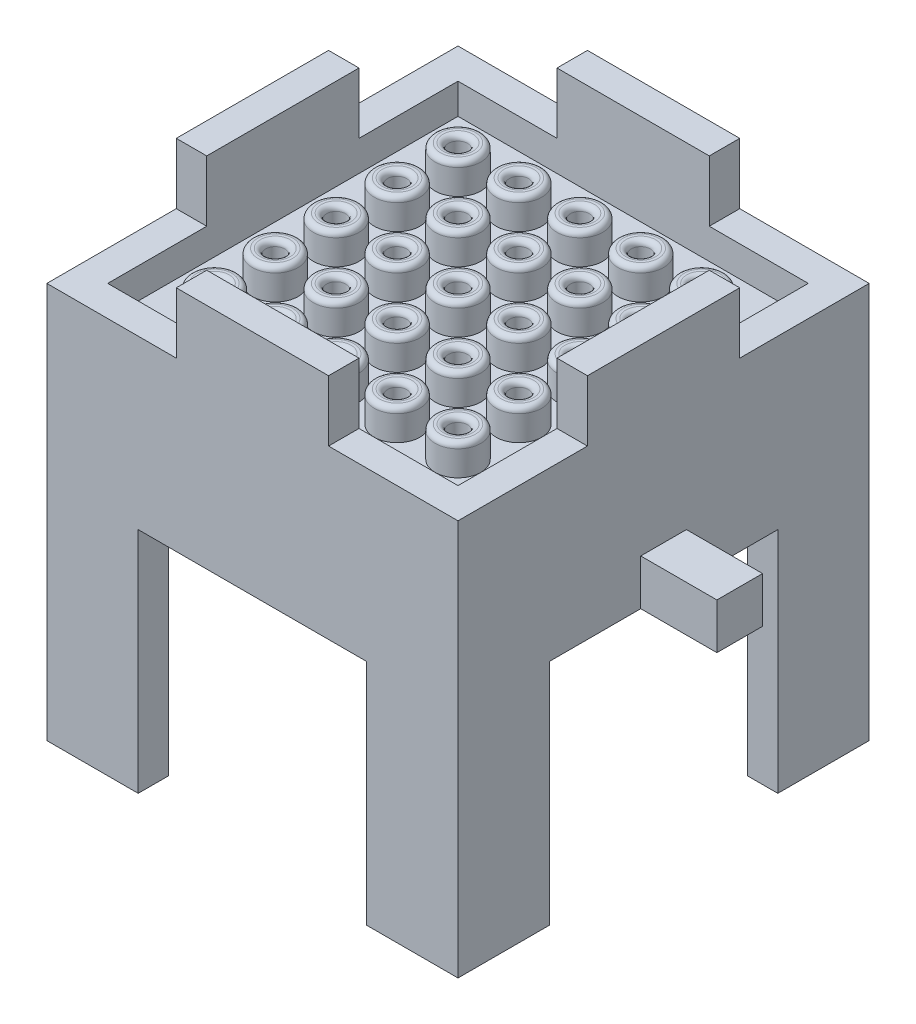
SolidWorks part; units mm, degrees
ref_plane "Front Plane" through (0, 0, 0) normal (0, 0, 1) x (1, 0, 0)
ref_plane "Top Plane" through (0, 0, 0) normal (0, 1, 0) x (1, 0, 0)
ref_plane "Right Plane" through (0, 0, 0) normal (1, 0, 0) x (0, 0, -1)
sketch "Sketch1" plane through (0, 0, 0) normal (0, 1, 0) x (1, 0, 0)
  line L0 (-13.5, 13.5) -> (13.5, 13.5)
  line L1 (-11.5, -11.5) -> (11.5, -11.5)
  line L2 (-11.5, -11.5) -> (-11.5, 11.5)
  line L3 (-11.5, 11.5) -> (11.5, 11.5)
  line L4 (11.5, -11.5) -> (11.5, 11.5)
  line L5 (-11.5, -11.5) -> (11.5, 11.5) construction
  line L6 (-11.5, 11.5) -> (11.5, -11.5) construction
  line L7 (13.5, -13.5) -> (13.5, 13.5)
  line L8 (-13.5, -13.5) -> (13.5, -13.5)
  line L9 (-13.5, -13.5) -> (-13.5, 13.5)
  point P0 (0, 0)
  dimension "D1" = 23
  dimension "D2" = 2
extrude "Boss-Extrude1" add sketch "Sketch1" along normal blind 2
sketch "Sketch2" plane through (0, 0, 0) normal (0, -1, 0) x (1, 0, 0)
  line L1 (-13.5, 13.5) -> (13.5, 13.5)
  line L2 (-13.5, 13.5) -> (-13.5, -13.5)
  line L3 (-13.5, -13.5) -> (13.5, -13.5)
  line L4 (13.5, 13.5) -> (13.5, -13.5)
  line L5 (-13.5, 13.5) -> (13.5, -13.5) construction
  line L6 (-13.5, -13.5) -> (13.5, 13.5) construction
  point P0 (0, 0)
extrude "Boss-Extrude2" add sketch "Sketch2" along normal blind 2
sketch "Sketch3" plane through (0, -2, 0) normal (0, -1, 0) x (1, 0, 0)
  line L0 (-11.5, 11.5) -> (11.5, 11.5)
  line L1 (-13.5, -13.5) -> (13.5, -13.5)
  line L2 (-13.5, -13.5) -> (-13.5, 13.5)
  line L3 (-13.5, 13.5) -> (13.5, 13.5)
  line L4 (13.5, -13.5) -> (13.5, 13.5)
  line L5 (-13.5, -13.5) -> (13.5, 13.5) construction
  line L6 (-13.5, 13.5) -> (13.5, -13.5) construction
  line L7 (11.5, -11.5) -> (11.5, 11.5)
  line L8 (-11.5, -11.5) -> (11.5, -11.5)
  line L9 (-11.5, -11.5) -> (-11.5, 11.5)
  point P0 (0, 0)
  dimension "D1" = 2
extrude "Boss-Extrude3" add sketch "Sketch3" along normal blind 5
sketch "Sketch6" plane through (0, 0, 0) normal (0, 1, 0) x (1, 0, 0)
  line L0 (11.5, -11.5) -> (11.5, 11.5) construction
  line L1 (11.5, 11.5) -> (-11.5, 11.5) construction
  circle A0 centre (8, 8) radius 1.5
  dimension "D2" = 3
  dimension "D1" = 3.5
  dimension "D3" = 3.5
extrude "Boss-Extrude5" add sketch "Sketch6" along normal blind 2
sketch "Sketch7" plane through (0, 2, 0) normal (0, 1, 0) x (1, 0, 0)
  circle A0 centre (8, 8) radius 0.625
  dimension "D1" = 1.25
extrude "Cut-Extrude2" cut sketch "Sketch7" against normal up to next (4 mm away)
fillet "Fillet3" radius 0.35 2 edges at (8, 2, -6.5) (8, 2, -7.375)
pattern_linear "LPattern1" count 5 spacing 4 along (0, 0, 1) count 5 spacing 4 along (-1, 0, 0) of "Boss-Extrude5", "Cut-Extrude2", "Fillet3"
sketch "Sketch11" plane through (0, -2, 0) normal (0, -1, 0) x (1, 0, 0)
  line L0 (11.5, 11.5) -> (-11.5, 11.5) construction
  line L1 (-11.5, 11.5) -> (-11.5, -11.5) construction
  circle A0 centre (-9.9, 9.9) radius 0.75
  dimension "D1" = 1.5
  dimension "D3" = 1.6
  dimension "D2" = 1.6
extrude "Boss-Extrude8" add sketch "Sketch11" along normal up to surface (5 mm away) up to face at (0, -7, 0)
pattern_linear "LPattern2" count 6 spacing 4 along (1, 0, 0) count 6 spacing 4 along (0, 0, -1) of "Boss-Extrude8"
sketch "Sketch8" plane through (0, -7, 0) normal (0, -1, 0) x (1, 0, 0)
  line L1 (-13.5, -13.5) -> (13.5, -13.5)
  line L2 (-13.5, -13.5) -> (-13.5, 13.5)
  line L3 (-13.5, 13.5) -> (13.5, 13.5)
  line L4 (13.5, -13.5) -> (13.5, 13.5)
  line L5 (-13.5, -13.5) -> (13.5, 13.5) construction
  line L6 (-13.5, 13.5) -> (13.5, -13.5) construction
  point P0 (0, 0)
extrude "Boss-Extrude6" add sketch "Sketch8" along normal blind 2
sketch "Sketch9" plane through (0, -9, 0) normal (0, -1, 0) x (1, 0, 0)
  circle A0 centre (0, 0) radius 4.25
  dimension "D1" = 8.5
extrude "Cut-Extrude3" cut sketch "Sketch9" against normal blind 7
sketch "Sketch10" plane through (0, 2, 0) normal (0, 1, 0) x (1, 0, 0)
  line L0 (-13.5, 0) -> (-11.5, 0) construction
  line L1 (-13.5, 13.5) -> (-13.5, -13.5) construction
  line L2 (-11.5, 11.5) -> (-11.5, -11.5) construction
  line L4 (-11.5, 5) -> (-13.5, 5)
  line L5 (-11.5, 5) -> (-11.5, -5)
  line L6 (-11.5, -5) -> (-13.5, -5)
  line L7 (-13.5, 5) -> (-13.5, -5)
  line L8 (-11.5, 5) -> (-13.5, -5) construction
  line L9 (-11.5, -5) -> (-13.5, 5) construction
  point P6 (-12.5, 0)
  dimension "D1" = 10
extrude "Boss-Extrude7" add sketch "Sketch10" along normal blind 4
pattern_circular "CirPattern1" count 4 over 360 about axis through (0, 0, 0) along (0, 1, 0) of "Boss-Extrude7"
sketch "Sketch12" plane through (-13.5, 0, 0) normal (-1, 0, 0) x (0, 0, 1)
  line L0 (13.5, -9) -> (-13.5, -9) construction
  line L1 (1.5, -6) -> (-1.5, -6)
  line L2 (1.5, -6) -> (1.5, -9)
  line L3 (1.5, -9) -> (-1.5, -9)
  line L4 (-1.5, -6) -> (-1.5, -9)
  line L5 (1.5, -6) -> (-1.5, -9) construction
  line L6 (1.5, -9) -> (-1.5, -6) construction
  line L7 (0, 0) -> (0, -9) construction
  point P0 (0, -7.5)
  dimension "D1" = 3
extrude "Boss-Extrude9" add sketch "Sketch12" along normal blind 5
pattern_circular "CirPattern2" count 2 over 360 about axis through (0, 0, 0) along (0, 1, 0) of "Boss-Extrude9"
sketch "Sketch13" plane through (0, -9, 0) normal (0, -1, 0) x (1, 0, 0)
  line L1 (-11.5, 7.5) -> (-13.5, 7.5)
  line L2 (-11.5, 7.5) -> (-11.5, 11.5)
  line L4 (-13.5, 7.5) -> (-13.5, 13.5)
  line L7 (-7.5, 11.5) -> (-11.5, 11.5)
  line L8 (-7.5, 11.5) -> (-7.5, 13.5)
  line L9 (-7.5, 13.5) -> (-13.5, 13.5)
  line L10 (-13.5, 11.6254) -> (-13.5, 13.5)
  point P0 (-12.424, 10.272)
  point P6 (-10.5717, 12.5239)
  line M7 (13.5, 13.5) -> (-13.5, 13.5)
  line M8 (-13.5, 13.5) -> (-13.5, 1.5)
  dimension "D1" = 2
  dimension "D2" = 6
extrude "Boss-Extrude10" add sketch "Sketch13" along normal blind 15 contours L7 L8 L4 L1 L2 M7 M8
pattern_circular "CirPattern3" count 4 over 360 about axis through (0, 0, 0) along (0, 1, 0) of "Boss-Extrude10"
equation "\"D3@Sketch6\"=\"D1@Sketch6\""
equation "\"D3@Sketch11\"=\"D2@Sketch11\""
